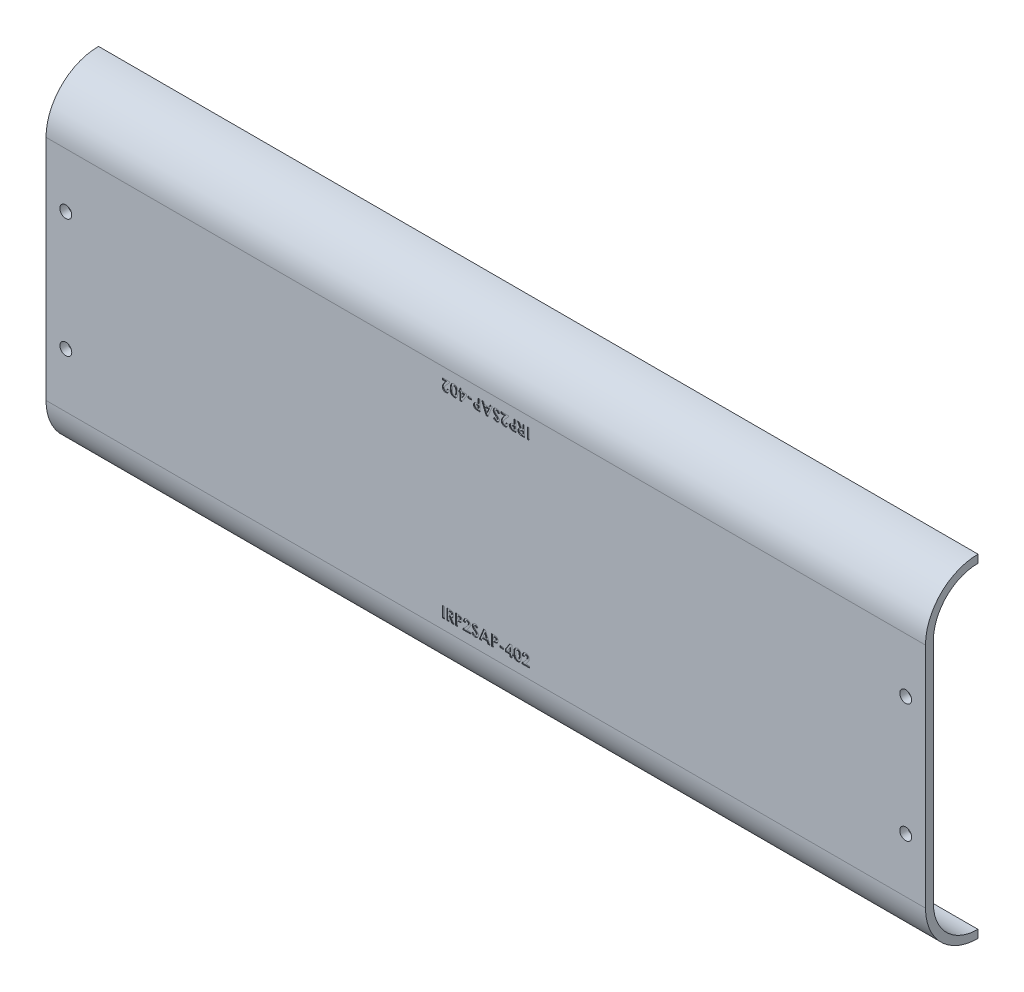
SolidWorks part; units mm, degrees
material "AISI 316 Stainless Steel Sheet (SS)"
ref_plane "Front" through (0, 0, 0) normal (0, 0, 1) x (1, 0, 0)
ref_plane "Top" through (0, 0, 0) normal (0, 1, 0) x (1, 0, 0)
ref_plane "Right" through (0, 0, 0) normal (1, 0, 0) x (0, 0, -1)
sketch "Sketch1" plane through (0, 0, 0) normal (1, 0, 0) x (0, 0, -1)
  line L0 (-16.8275, 0) -> (-16.8275, -73.025)
  line L1 (0, -89.8525) -> (0, -87.3125)
  line L2 (0, 16.8275) -> (0, 14.2875)
  line L3 (-14.2875, 0) -> (-14.2875, -73.025)
  arc A0 (0, 16.8275) -> (-16.8275, 0) centre (0, 0) ccw
  arc A1 (-16.8275, -73.025) -> (0, -89.8525) centre (0, -73.025) ccw
  arc A2 (0, 14.2875) -> (-14.2875, 0) centre (0, 0) ccw
  arc A3 (-14.2875, -73.025) -> (0, -87.3125) centre (0, -73.025) ccw
  dimension "D2" = 14.2875
  dimension "D1" = 2.54
  dimension "D3" = 73.025
extrude "Boss-Extrude1" add sketch "Sketch1" along normal blind 281.8834
sketch "Sketch2" plane through (0, 0, 16.8275) normal (0, 0, 1) x (1, 0, 0)
  line L0 (6.35, -17.4625) -> (275.5334, -17.4625) construction
  line L1 (275.5334, -17.4625) -> (275.5334, -55.5625) construction
  line L2 (275.5334, -55.5625) -> (6.35, -55.5625) construction
  line L3 (6.35, -55.5625) -> (6.35, -17.4625) construction
  line L4 (0, -36.5125) -> (6.35, -36.5125) construction
  line L5 (0, 0) -> (0, -73.025) construction
  line L6 (6.35, -36.5125) -> (140.9417, -17.4625) construction
  line L7 (140.9417, -17.4625) -> (140.9417, 0) construction
  line L8 (281.8834, 0) -> (0, 0) construction
  circle A0 centre (6.35, -17.4625) radius 1.905
  circle A1 centre (6.35, -55.5625) radius 1.905
  circle A2 centre (275.5334, -17.4625) radius 1.905
  circle A3 centre (275.5334, -55.5625) radius 1.905
  dimension "D3" = 3.81
  dimension "D1" = 38.1
  dimension "D2" = 269.1834
extrude "Cut-Extrude1" cut sketch "Sketch2" against normal through all
sketch "Sketch3" plane through (0, 0, 16.8275) normal (0, 0, 1) x (1, 0, 0)
  line L0 (0, -69.85) -> (281.8834, -69.85) construction
  line L1 (0, 0) -> (0, -73.025) construction
  line L2 (281.8834, 0) -> (281.8834, -73.025) construction
  line L3 (281.8834, -73.025) -> (0, -73.025) construction
  text T0 "<b>IRP2SAP-402</b>"
  dimension "D1" = 3.175
extrude "Cut-Extrude2" cut sketch "Sketch3" against normal blind 0.254
sketch "Sketch4" plane through (0, 0, 16.8275) normal (0, 0, 1) x (1, 0, 0)
  line L0 (0, -3.175) -> (281.8834, -3.175) construction
  line L1 (0, 0) -> (0, -73.025) construction
  line L2 (281.8834, 0) -> (281.8834, -73.025) construction
  line L3 (281.8834, 0) -> (0, 0) construction
  text T0 "<b>IRP2SAP-402</b>"
  dimension "D1" = 3.175
extrude "Cut-Extrude3" cut sketch "Sketch4" against normal blind 0.254
